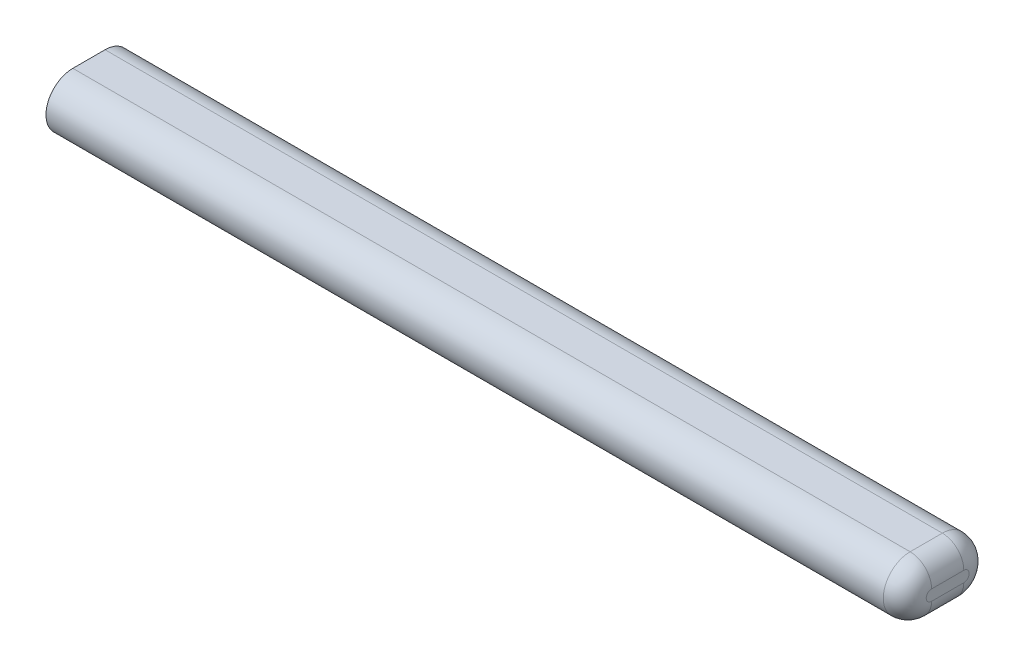
SolidWorks part; units mm, degrees
ref_plane "Alzado" through (0, 0, 0) normal (0, 0, 1) x (1, 0, 0)
ref_plane "Planta" through (0, 0, 0) normal (0, 1, 0) x (1, 0, 0)
ref_plane "Vista lateral" through (0, 0, 0) normal (1, 0, 0) x (0, 0, -1)
sketch "Croquis1" plane through (0, 0, 0) normal (1, 0, 0) x (0, 0, -1)
  line L0 (0, 0) -> (15, 0) construction
  line L1 (0, 12.5) -> (15, 12.5)
  line L2 (0, -12.5) -> (15, -12.5)
  line L3 (-12.5, 0) -> (27.5, 0) construction
  arc A0 (0, 12.5) -> (0, -12.5) centre (0, 0) ccw
  arc A1 (15, -12.5) -> (15, 12.5) centre (15, 0) ccw
  point P3 (7.5, 0)
  dimension "D1" = 40
  dimension "D2" = 25
extrude "Saliente-Extruir1" add sketch "Croquis1" along normal blind 400
fillet "Redondeo1" radius 10 4 edges at (400, 12.5, -7.5) (400, 0, -27.5) (400, -12.5, -7.5) (400, 0, 12.5)
